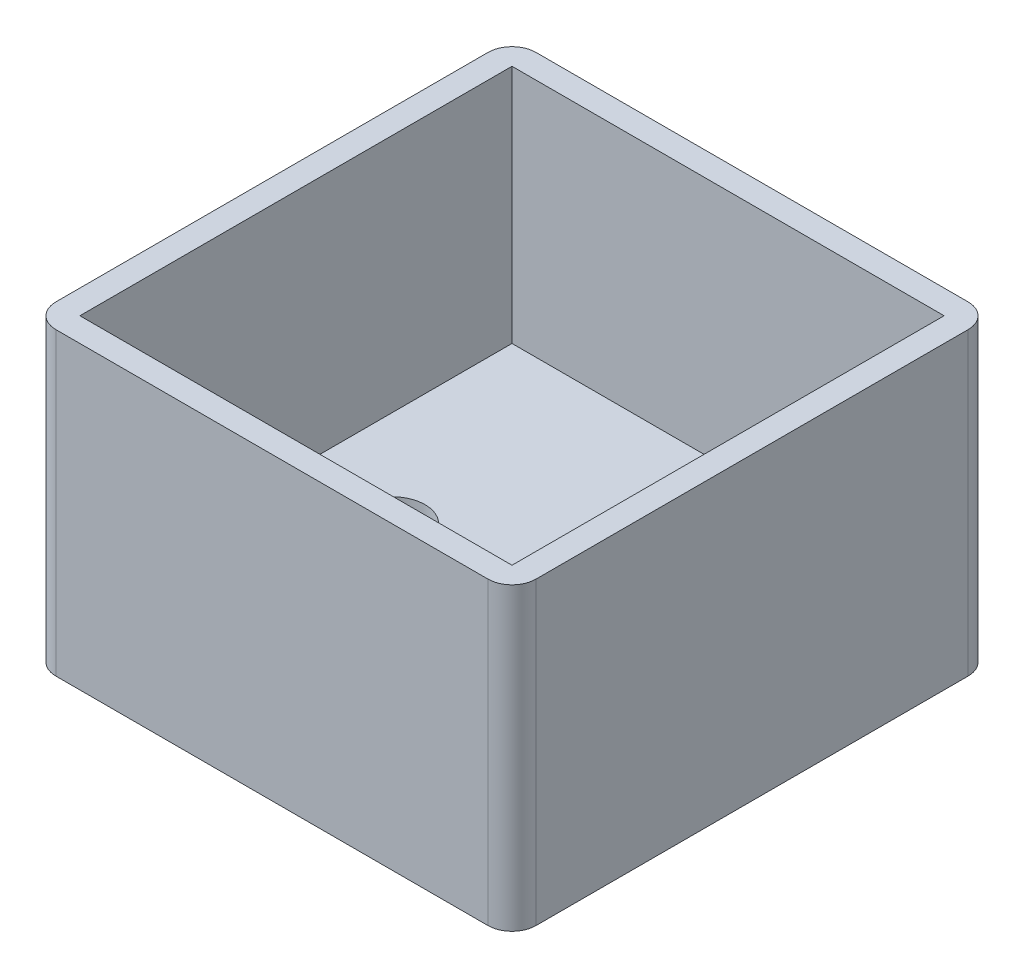
SolidWorks part; units mm, degrees
ref_plane "Front Plane" through (0, 0, 0) normal (0, 0, 1) x (1, 0, 0)
ref_plane "Top Plane" through (0, 0, 0) normal (0, 1, 0) x (1, 0, 0)
ref_plane "Right Plane" through (0, 0, 0) normal (1, 0, 0) x (0, 0, -1)
sketch "Sketch1" plane through (0, 0, 0) normal (0, 1, 0) x (1, 0, 0)
  line L0 (0, 20) -> (40, 20) construction
  line L1 (2, 0) -> (38, 0)
  line L2 (0, 2) -> (0, 38)
  line L3 (2, 40) -> (38, 40)
  line L4 (40, 2) -> (40, 38)
  line L5 (20, 40) -> (20, 0) construction
  circle A0 centre (10, 20) radius 2.75
  circle A1 centre (30, 20) radius 2.75
  arc A2 (0, 2) -> (2, 0) centre (2, 2) ccw
  arc A3 (38, 0) -> (40, 2) centre (38, 2) ccw
  arc A4 (40, 38) -> (38, 40) centre (38, 38) ccw
  arc A5 (2, 40) -> (0, 38) centre (2, 38) ccw
  point P15 (0, 0)
  point P18 (40, 0)
  dimension "D3" = 5.5
  dimension "D4" = 2
  dimension "D1" = 40
  dimension "D2" = 20
extrude "base" add sketch "Sketch1" along normal blind 5
sketch "Sketch3" plane through (0, 5, 0) normal (0, 1, 0) x (1, 0, 0)
  line L8 (2, 38) -> (2, 2)
  line L9 (2, 2) -> (38, 2)
  line L10 (38, 2) -> (38, 38)
  line L11 (38, 38) -> (2, 38)
  line L12 (2, 38) -> (2, 2)
  line L13 (2, 2) -> (38, 2)
  line L14 (38, 2) -> (38, 38)
  line L15 (38, 38) -> (2, 38)
  line L20 (0, 38) -> (0, 2)
  line L21 (2, 0) -> (38, 0)
  line L22 (40, 2) -> (40, 38)
  line L23 (38, 40) -> (2, 40)
  line L24 (0, 38) -> (0, 2)
  line L25 (2, 0) -> (38, 0)
  line L26 (40, 2) -> (40, 38)
  line L27 (38, 40) -> (2, 40)
  arc A4 (0, 2) -> (2, 0) centre (2, 2) ccw
  arc A5 (0, 2) -> (2, 0) centre (2, 2) ccw
  arc A6 (38, 0) -> (40, 2) centre (38, 2) ccw
  arc A7 (38, 0) -> (40, 2) centre (38, 2) ccw
  arc A8 (40, 38) -> (38, 40) centre (38, 38) ccw
  arc A9 (40, 38) -> (38, 40) centre (38, 38) ccw
  arc A10 (2, 40) -> (0, 38) centre (2, 38) ccw
  arc A11 (2, 40) -> (0, 38) centre (2, 38) ccw
  dimension "D1" = 2
  dimension "D2" = 0
extrude "Boss-Extrude2" add sketch "Sketch3" along normal blind 20
